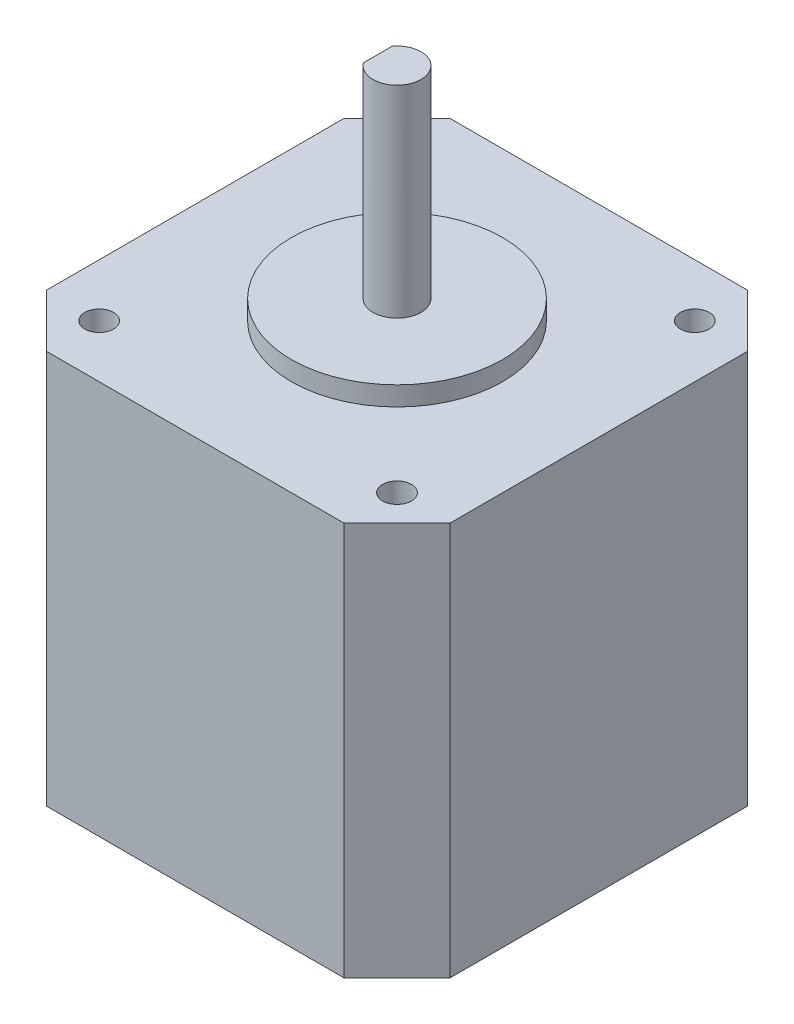
SolidWorks part; units mm, degrees
ref_plane "Front Plane" through (0, 0, 0) normal (0, 0, 1) x (1, 0, 0)
ref_plane "Top Plane" through (0, 0, 0) normal (0, 1, 0) x (1, 0, 0)
ref_plane "Right Plane" through (0, 0, 0) normal (1, 0, 0) x (0, 0, -1)
sketch "Sketch1" plane through (0, 0, 0) normal (0, 1, 0) x (1, 0, 0)
  line L0 (-15.5, -21) -> (15.5, -21)
  line L1 (-15.5, 21) -> (15.5, 21)
  line L2 (21, 15.5) -> (21, -15.5)
  line L3 (-21, 15.5) -> (-21, -15.5)
  line L4 (-15.5, 21) -> (-21, 15.5)
  line L5 (15.5, 21) -> (21, 15.5)
  line L6 (-21, -15.5) -> (-15.5, -21)
  line L7 (15.5, -21) -> (21, -15.5)
extrude "Boss-Extrude1" add sketch "Sketch1" along normal mid plane 23
sketch "Sketch3" plane through (0, -11.5, 0) normal (0, -1, 0) x (1, 0, 0)
  line L0 (-21, 15.5) -> (-15.5, 21) construction
  line L1 (15.5, 21) -> (21, 15.5) construction
  line L2 (15.5, -21) -> (-15.5, -21) construction
  line L3 (21, 15.5) -> (21, -15.5) construction
  line L4 (21, -15.5) -> (15.5, -21) construction
  line L5 (-15.5, -21) -> (-21, -15.5) construction
  line L6 (-21, -15.5) -> (-21, 15.5) construction
  line L7 (-15.5, 21) -> (15.5, 21) construction
  line L8 (-15.5, 21) -> (-21, 15.5)
  line L9 (-21, 15.5) -> (-21, -15.5)
  line L10 (-21, -15.5) -> (-15.5, -21)
  line L11 (-15.5, -21) -> (15.5, -21)
  line L12 (15.5, -21) -> (21, -15.5)
  line L13 (21, -15.5) -> (21, 15.5)
  line L14 (21, 15.5) -> (15.5, 21)
  line L15 (15.5, 21) -> (-15.5, 21)
  line L16 (-15.5, 21) -> (-21, 15.5)
  line L17 (-21, 15.5) -> (-21, -15.5)
  line L18 (-21, -15.5) -> (-15.5, -21)
  line L19 (-15.5, -21) -> (15.5, -21)
  line L20 (15.5, -21) -> (21, -15.5)
  line L21 (21, -15.5) -> (21, 15.5)
  line L22 (21, 15.5) -> (15.5, 21)
  line L23 (15.5, 21) -> (-15.5, 21)
  line L24 (15.5, 21) -> (21, 15.5)
  line L25 (15.5, -21) -> (-15.5, -21)
  line L26 (21, 15.5) -> (21, -15.5)
  line L27 (21, -15.5) -> (15.5, -21)
  line L28 (-15.5, -21) -> (-21, -15.5)
  line L29 (-21, -15.5) -> (-21, 15.5)
  line L30 (-21, 15.5) -> (-15.5, 21)
  line L31 (-15.5, 21) -> (15.5, 21)
  line M9 (-15.5, 21) -> (-21, 15.5)
  line M10 (-21, 15.5) -> (-21, -15.5)
  line M11 (-21, -15.5) -> (-15.5, -21)
  line M12 (-15.5, -21) -> (15.5, -21)
  line M13 (15.5, -21) -> (21, -15.5)
  line M14 (21, -15.5) -> (21, 15.5)
  line M15 (21, 15.5) -> (15.5, 21)
  line M16 (15.5, 21) -> (-15.5, 21)
  dimension "D1" = 0
extrude "Boss-Extrude2" add sketch "Sketch3" along normal blind 10 contours M16 M9 M10 M11 M12 M13 M14 M15
sketch "Sketch4" plane through (0, 11.5, 0) normal (0, 1, 0) x (1, 0, 0)
  line L0 (-15.5, -21) -> (15.5, -21)
  line L1 (-15.5, 21) -> (15.5, 21)
  line L2 (21, 15.5) -> (21, -15.5)
  line L3 (-21, 15.5) -> (-21, -15.5)
  line L4 (-15.5, 21) -> (-21, 15.5)
  line L5 (15.5, 21) -> (21, 15.5)
  line L6 (-21, -15.5) -> (-15.5, -21)
  line L7 (15.5, -21) -> (21, -15.5)
  circle A0 centre (-15.5, 15.5) radius 1.5
  circle A1 centre (15.5, 15.5) radius 1.5
  circle A2 centre (-15.5, -15.5) radius 1.5
  circle A3 centre (15.5, -15.5) radius 1.5
extrude "Boss-Extrude3" add sketch "Sketch4" along normal blind 8
sketch "Sketch5" plane through (0, 19.5, 0) normal (0, 1, 0) x (1, 0, 0)
  circle A0 centre (0, 0) radius 11
extrude "Boss-Extrude4" add sketch "Sketch5" along normal blind 2
sketch "Sketch6" plane through (0, 21.5, 0) normal (0, 1, 0) x (1, 0, 0)
  circle A0 centre (0, 0) radius 2.5
extrude "Boss-Extrude5" add sketch "Sketch6" along normal blind 21
sketch "Sketch9" plane through (0, 42.5, 0) normal (0, 1, 0) x (1, 0, 0)
  line L2 (-2, 1.5) -> (-2, -1.5)
  arc A0 (-2, 1.5) -> (-2, -1.5) centre (0, 0) ccw
extrude "Cut-Extrude1" cut sketch "Sketch9" against normal blind 18
